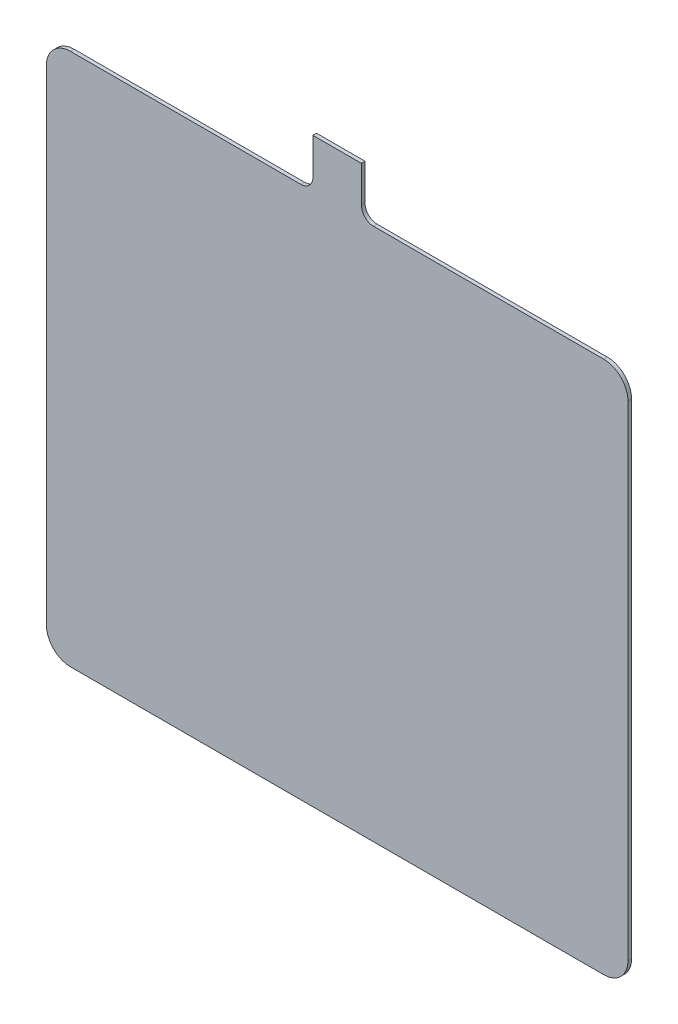
SolidWorks part; units mm, degrees
ref_plane "Plan de face" through (0, 0, 0) normal (0, 0, 1) x (1, 0, 0)
ref_plane "Plan de dessus" through (0, 0, 0) normal (0, 1, 0) x (1, 0, 0)
ref_plane "Plan de droite" through (0, 0, 0) normal (1, 0, 0) x (0, 0, -1)
sketch "Esquisse1" plane through (0, 0, 0) normal (0, 0, 1) x (1, 0, 0)
  line L1 (-220, 295) -> (-30, 295)
  line L2 (-240, 275) -> (-240, -125)
  line L3 (-220, -145) -> (220, -145)
  line L4 (240, 275) -> (240, -125)
  line L8 (-340, 335) -> (340, 335) construction
  line L9 (30, 295) -> (220, 295)
  line L10 (-20, 335) -> (20, 335)
  line L11 (-20, 305) -> (-20, 335)
  line L13 (20, 305) -> (20, 335)
  arc A0 (-30, 295) -> (-20, 305) centre (-30, 305) ccw
  arc A1 (30, 295) -> (20, 305) centre (30, 305) cw
  arc A4 (-240, -125) -> (-220, -145) centre (-220, -125) ccw
  arc A5 (220, -145) -> (240, -125) centre (220, -125) ccw
  arc A6 (220, 295) -> (240, 275) centre (220, 275) cw
  arc A7 (-220, 295) -> (-240, 275) centre (-220, 275) ccw
  dimension "D8" = 10
  dimension "D9" = 20
extrude "Boss.-Extru.1" add sketch "Esquisse1" along normal blind 3
